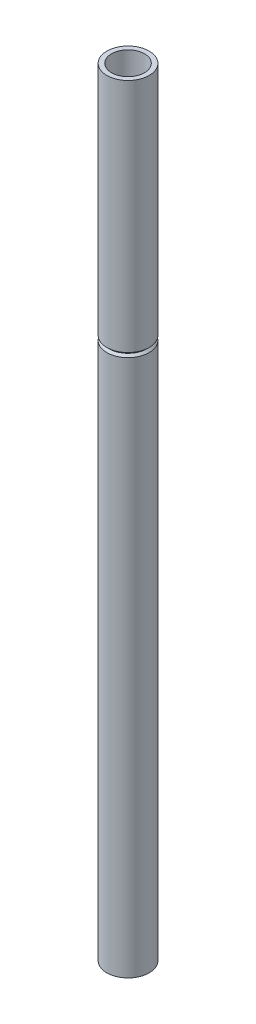
SolidWorks part; units mm, degrees
ref_plane "Front Plane" through (0, 0, 0) normal (0, 0, 1) x (1, 0, 0)
ref_plane "Top Plane" through (0, 0, 0) normal (0, 1, 0) x (1, 0, 0)
ref_plane "Right Plane" through (0, 0, 0) normal (1, 0, 0) x (0, 0, -1)
sketch "Sketch1" plane through (0, 0, 0) normal (0, 0, 1) x (1, 0, 0)
  line L0 (0.68, 25) -> (0.68, 17.4207)
  line L1 (0.68, 17.4207) -> (0.6093, 17.35)
  line L2 (0.6093, 17.35) -> (0.68, 17.2793)
  line L3 (0.68, 17.2793) -> (0.68, 0)
  line L4 (0, 0) -> (0, 4.4071) construction
  line L5 (0.68, 0) -> (0.1466, -0.1873)
  dimension "D1" = 0.68
  dimension "D2" = 25
  dimension "D3" = 7.65
  dimension "D4" = 0.1
revolve "Revolve-Thin1" add sketch "Sketch1" angle 360 about L4
